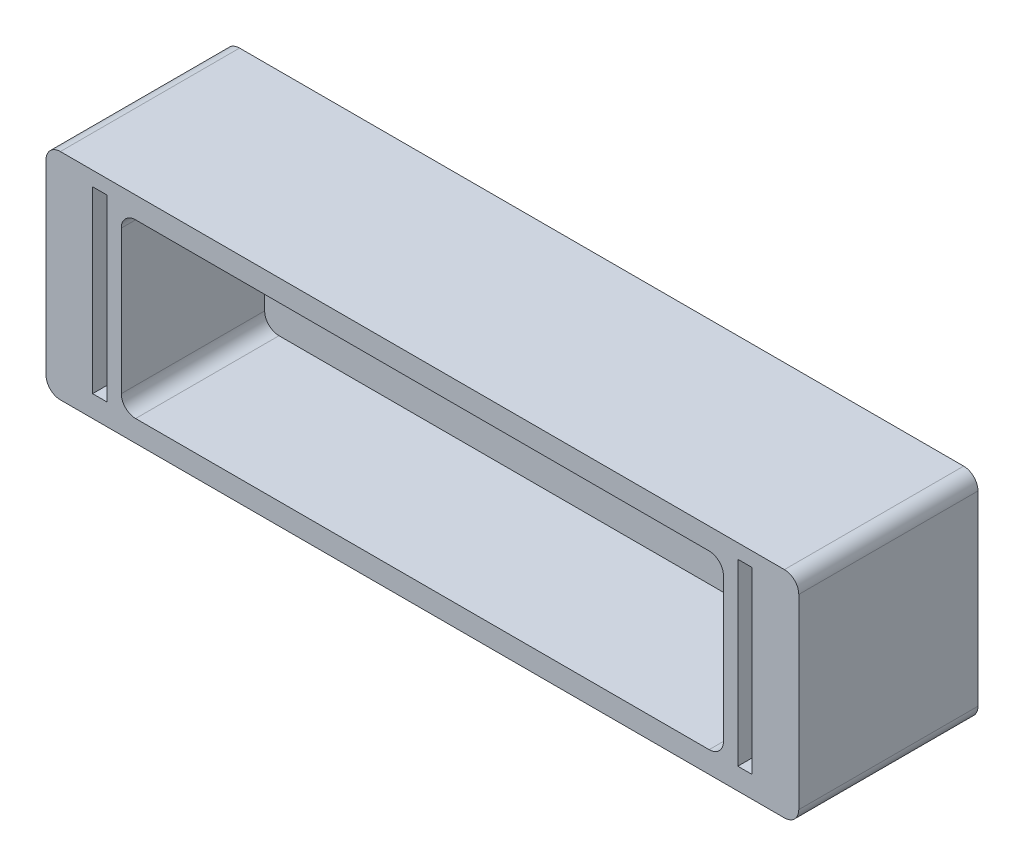
SolidWorks part; units mm, degrees
ref_plane "Front Plane" through (0, 0, 0) normal (0, 0, 1) x (1, 0, 0)
ref_plane "Top Plane" through (0, 0, 0) normal (0, 1, 0) x (1, 0, 0)
ref_plane "Right Plane" through (0, 0, 0) normal (1, 0, 0) x (0, 0, -1)
sketch "Esquisse1" plane through (0, 0, 0) normal (0, 0, 1) x (1, 0, 0)
  line L1 (-41.846, 49.5477) -> (63.154, 49.5477)
  line L2 (-41.846, 49.5477) -> (-41.846, 19.5477)
  line L3 (-41.846, 19.5477) -> (63.154, 19.5477)
  line L4 (63.154, 49.5477) -> (63.154, 19.5477)
  dimension "D1" = 105
  dimension "D2" = 30
extrude "Boss.-Extru.1" add sketch "Esquisse1" along normal blind 25
sketch "Esquisse2" plane through (0, 0, 25) normal (0, 0, 1) x (1, 0, 0)
  line L0 (-12.5843, 37.5477) -> (-48.9959, 37.5477) construction
  line L1 (-48.9959, 37.5477) -> (69.7119, 37.5477) construction
  line L2 (10.654, 57.8076) -> (10.654, 9.8509) construction
  line L4 (-35.346, 47.5477) -> (-33.346, 47.5477)
  line L5 (-35.346, 47.5477) -> (-35.346, 22.5477)
  line L6 (-35.346, 22.5477) -> (-33.346, 22.5477)
  line L7 (-33.346, 47.5477) -> (-33.346, 22.5477)
  line L9 (-41.846, 19.5477) -> (63.154, 19.5477) construction
  line L10 (54.654, 47.5477) -> (54.654, 22.5477)
  line L11 (56.654, 22.5477) -> (54.654, 22.5477)
  line L12 (56.654, 47.5477) -> (56.654, 22.5477)
  line L13 (56.654, 47.5477) -> (54.654, 47.5477)
  line L14 (63.154, 19.5477) -> (63.154, 49.5477) construction
  point P9 (-34.346, 22.5477)
  dimension "D1" = 2
  dimension "D2" = 44
  dimension "D3" = 25
  dimension "D4" = 3
  dimension "D5" = 52.5
extrude "Enlèv. mat.-Extru.1" cut sketch "Esquisse2" against normal blind 24
fillet "Congé3" radius 12 2 edges at (55.654, 47.5477, 1) (55.654, 22.5477, 1)
fillet "Congé4" radius 12 2 edges at (-34.346, 47.5477, 1) (-34.346, 22.5477, 1)
sketch "Esquisse3" plane through (0, 0, 25) normal (0, 0, 1) x (1, 0, 0)
  line L0 (63.154, 49.5477) -> (-41.846, 49.5477) construction
  line L1 (-31.346, 46.5477) -> (52.654, 46.5477)
  line L2 (-31.346, 46.5477) -> (-31.346, 22.5477)
  line L3 (-31.346, 22.5477) -> (52.654, 22.5477)
  line L4 (52.654, 46.5477) -> (52.654, 22.5477)
  line L5 (-41.846, 19.5477) -> (63.154, 19.5477) construction
  line L6 (-33.346, 47.5477) -> (-33.346, 35.5477) construction
  line L7 (54.654, 47.5477) -> (54.654, 22.5477) construction
  dimension "D1" = 3
  dimension "D2" = 3
  dimension "D3" = 2
  dimension "D4" = 2
extrude "Enlèv. mat.-Extru.2" cut sketch "Esquisse3" against normal blind 20
fillet "Congé5" radius 2 5 edges at (52.654, 46.5477, 15) (52.654, 22.5477, 15) (63.154, 19.5477, 12.5) (63.154, 49.5477, 12.5) (-41.846, 49.5477, 12.5)
fillet "Congé6" radius 2 2 edges at (-31.346, 46.5477, 15) (-31.346, 22.5477, 15)
fillet "Congé7" radius 2 1 edges at (-41.846, 19.5477, 12.5)
